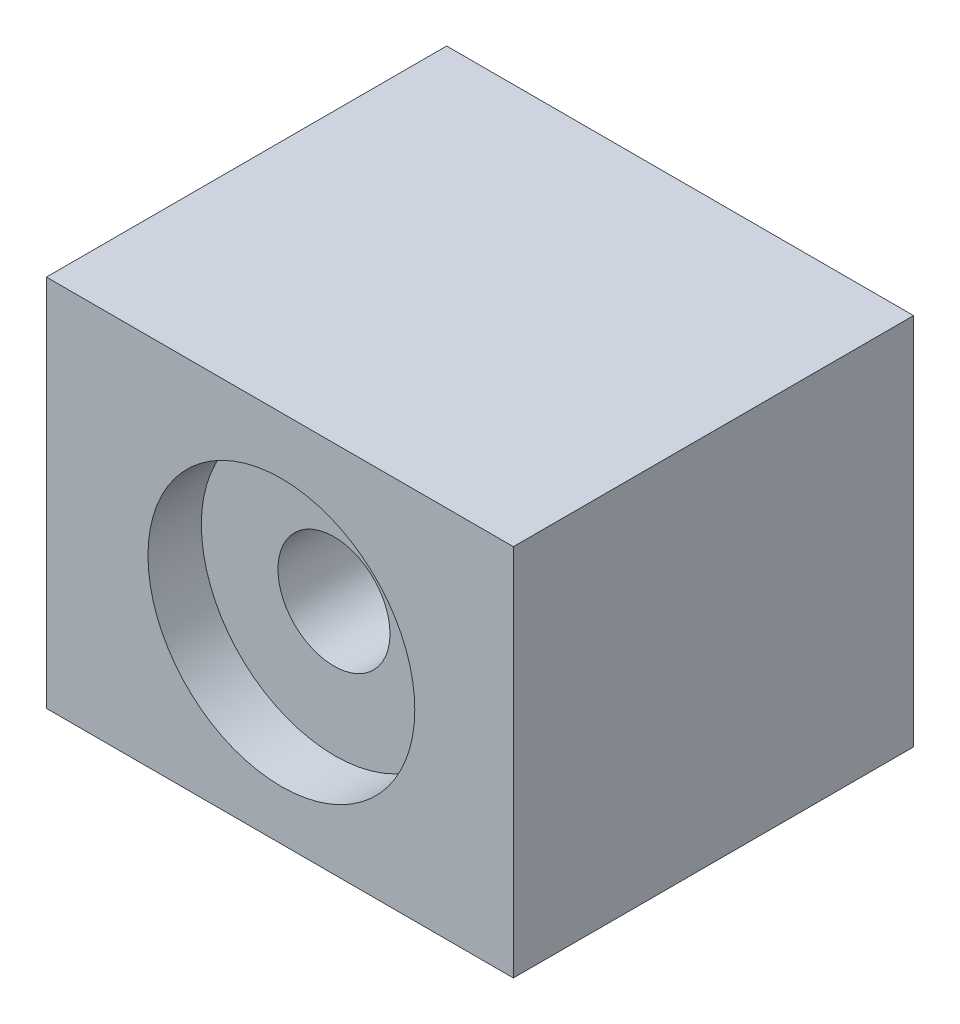
SolidWorks part; units mm, degrees
ref_plane "Front Plane" through (0, 0, 0) normal (0, 0, 1) x (1, 0, 0)
ref_plane "Top Plane" through (0, 0, 0) normal (0, 1, 0) x (1, 0, 0)
ref_plane "Right Plane" through (0, 0, 0) normal (1, 0, 0) x (0, 0, -1)
sketch "Sketch1" plane through (0, 0, 0) normal (0, 1, 0) x (1, 0, 0)
  line L1 (-20.1515, 10.7828) -> (14.8485, 10.7828)
  line L2 (-20.1515, 10.7828) -> (-20.1515, -19.2172)
  line L3 (-20.1515, -19.2172) -> (14.8485, -19.2172)
  line L4 (14.8485, 10.7828) -> (14.8485, -19.2172)
  line L5 (-20.1515, 10.7828) -> (14.8485, -19.2172) construction
  line L6 (-20.1515, -19.2172) -> (14.8485, 10.7828) construction
  point P4 (-2.6515, -4.2172)
  dimension "D1" = 35
  dimension "D2" = 30
extrude "Boss-Extrude1" add sketch "Sketch1" along normal blind 28
sketch "Sketch2" plane through (0, 0, 19.2172) normal (0, 0, 1) x (1, 0, 0)
  circle A0 centre (-2.5388, 13.7334) radius 10
  circle A1 centre (-2.5388, 13.7334) radius 4
extrude "Cut-Extrude1" cut sketch "Sketch2" against normal blind 4
sketch "Sketch4" plane through (0, 0, 19.2172) normal (0, 0, 1) x (1, 0, 0)
  circle A0 centre (-2.5976, 13.7231) radius 4.2
extrude "Cut-Extrude2" cut sketch "Sketch4" against normal blind 48
